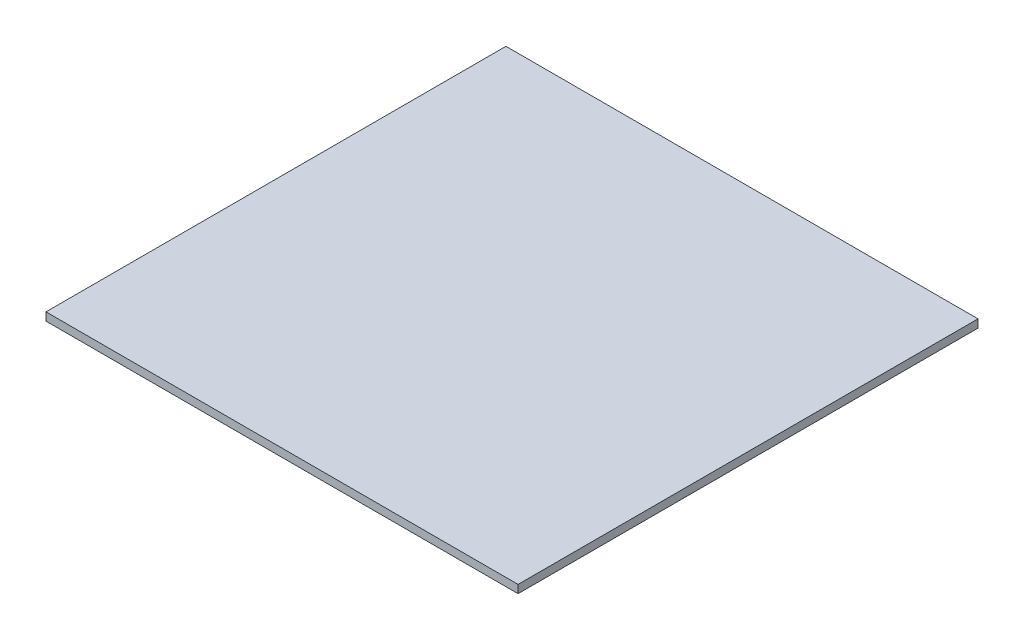
SolidWorks part; units mm, degrees
ref_plane "Front Plane" through (0, 0, 0) normal (0, 0, 1) x (1, 0, 0)
ref_plane "Top Plane" through (0, 0, 0) normal (0, 1, 0) x (1, 0, 0)
ref_plane "Right Plane" through (0, 0, 0) normal (1, 0, 0) x (0, 0, -1)
sketch "Sketch1" plane through (0, 20425, 0) normal (0, 1, 0) x (-1, 0, 0)
  line L0 (-10900, 0) -> (0, 0) construction
  line L1 (-10900, 5700) -> (-5050, 5700)
  line L2 (-10900, 5700) -> (-10900, 0)
  line L3 (-10900, 0) -> (-5050, 0)
  line L4 (-5050, 5700) -> (-5050, 0)
  dimension "D1" = 5850
extrude "Extrude1" add sketch "Sketch1" along normal blind 100
